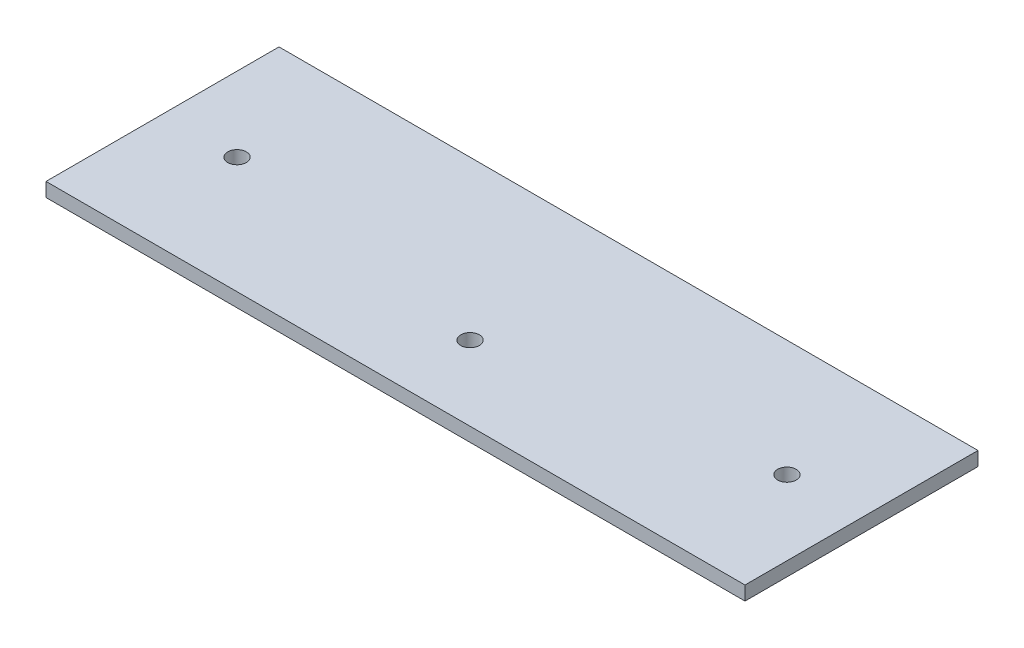
SolidWorks part; units mm, degrees
ref_plane "Front" through (0, 0, 0) normal (0, 0, 1) x (1, 0, 0)
ref_plane "Top" through (0, 0, 0) normal (0, 1, 0) x (1, 0, 0)
ref_plane "Right" through (0, 0, 0) normal (1, 0, 0) x (0, 0, -1)
sketch "Sketch1" plane through (0, 0, 0) normal (0, 1, 0) x (1, 0, 0)
  line L1 (75, 25) -> (-75, 25)
  line L2 (75, 25) -> (75, -25)
  line L3 (75, -25) -> (-75, -25)
  line L4 (-75, 25) -> (-75, -25)
  line L5 (75, 25) -> (-75, -25) construction
  line L6 (75, -25) -> (-75, 25) construction
  point P0 (0, 0)
  dimension "D1" = 50
  dimension "D2" = 150
extrude "Boss-Extrude1" add sketch "Sketch1" along normal blind 3
sketch "Sketch2" plane through (0, 3, 0) normal (0, 1, 0) x (1, 0, 0)
  line L0 (75, -25) -> (75, 25) construction
  circle A0 centre (59, 0) radius 2
  point P4 (75, 0)
  dimension "D1" = 4
  dimension "D2" = 16
extrude "Cut-Extrude1" cut sketch "Sketch2" against normal up to next (3 mm away)
mirror "Mirror1" about plane through (0, 0, 0) normal (1, 0, 0) of "Cut-Extrude1"
sketch "Sketch3" plane through (0, 3, 0) normal (0, 1, 0) x (1, 0, 0)
  line L0 (-75, -25) -> (75, -25) construction
  circle A0 centre (0, -9) radius 2
  point P5 (0, 0)
  dimension "D1" = 4
  dimension "D2" = 16
extrude "Cut-Extrude2" cut sketch "Sketch3" against normal up to next
